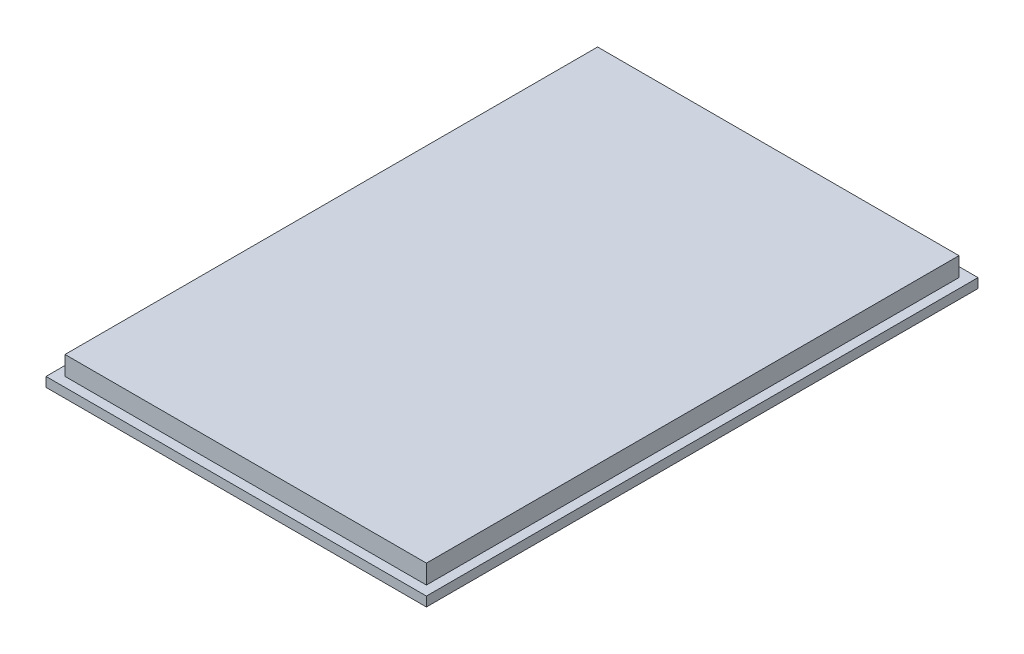
SolidWorks part; units mm, degrees
ref_plane "Front Plane" through (0, 0, 0) normal (0, 0, 1) x (1, 0, 0)
ref_plane "Top Plane" through (0, 0, 0) normal (0, 1, 0) x (1, 0, 0)
ref_plane "Right Plane" through (0, 0, 0) normal (1, 0, 0) x (0, 0, -1)
sketch "Sketch2" plane through (0, 0, 0) normal (0, 1, 0) x (1, 0, 0)
  line L1 (-100, 145) -> (100, 145)
  line L2 (-100, 145) -> (-100, -145)
  line L3 (-100, -145) -> (100, -145)
  line L4 (100, 145) -> (100, -145)
  line L5 (-100, 145) -> (100, -145) construction
  line L6 (-100, -145) -> (100, 145) construction
  point P0 (0, 0)
  dimension "D1" = 290
  dimension "D2" = 200
extrude "Boss-Extrude1" add sketch "Sketch2" along normal blind 5
sketch "Sketch3" plane through (0, 5, 0) normal (0, 1, 0) x (1, 0, 0)
  line L0 (-100, 145) -> (-100, -145) construction
  line L1 (-95, -140) -> (95, -140)
  line L2 (-95, -140) -> (-95, 140)
  line L3 (-95, 140) -> (95, 140)
  line L4 (95, -140) -> (95, 140)
  line L5 (-95, -140) -> (95, 140) construction
  line L6 (-95, 140) -> (95, -140) construction
  line L7 (100, 145) -> (-100, 145) construction
  point P0 (0, 0)
  dimension "D1" = 5
  dimension "D2" = 5
extrude "Boss-Extrude2" add sketch "Sketch3" along normal blind 10
